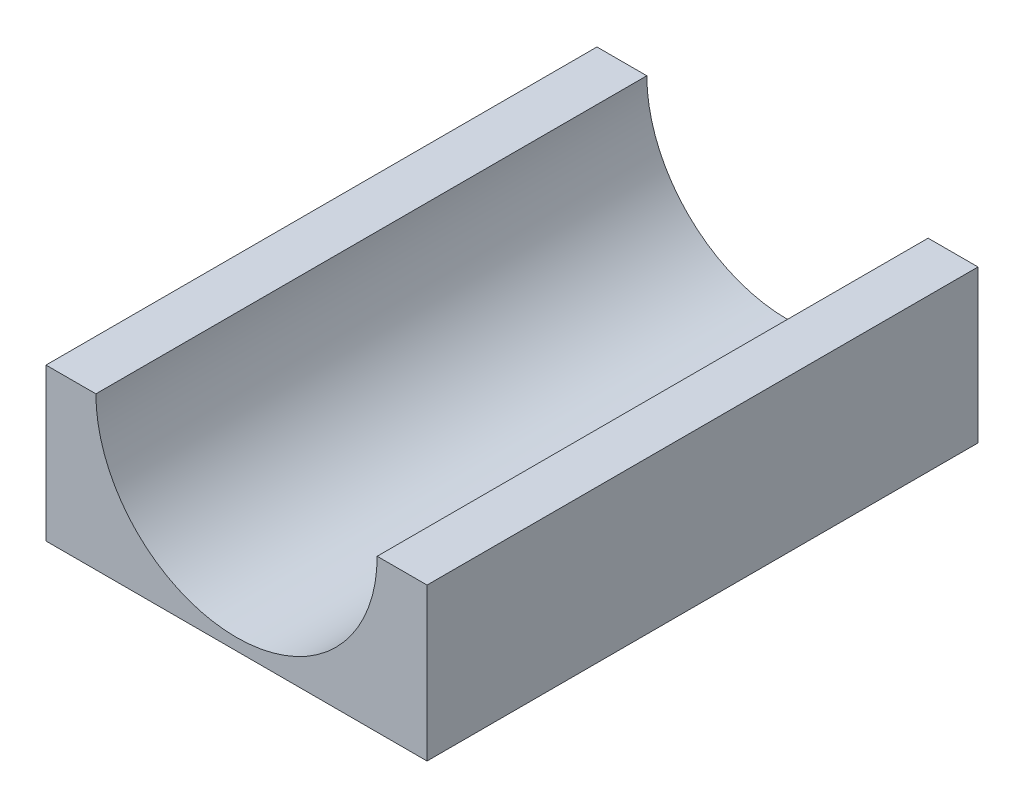
SolidWorks part; units mm, degrees
ref_plane "Front Plane" through (0, 0, 0) normal (0, 0, 1) x (1, 0, 0)
ref_plane "Top Plane" through (0, 0, 0) normal (0, 1, 0) x (1, 0, 0)
ref_plane "Right Plane" through (0, 0, 0) normal (1, 0, 0) x (0, 0, -1)
sketch "Sketch1" plane through (0, 0, 0) normal (0, 1, 0) x (1, 0, 0)
  line L1 (-25.4, 36.725) -> (25.4, 36.725)
  line L2 (-25.4, 36.725) -> (-25.4, -36.725)
  line L3 (-25.4, -36.725) -> (25.4, -36.725)
  line L4 (25.4, 36.725) -> (25.4, -36.725)
  point P4 (0, 36.725)
  point P6 (25.4, 0)
  dimension "D1" = 73.45
  dimension "D2" = 50.8
extrude "Boss-Extrude1" add sketch "Sketch1" along normal blind 20.32
sketch "Sketch2" plane through (0, 0, 36.725) normal (0, 0, 1) x (1, 0, 0)
  line L0 (-25.4, 20.32) -> (25.4, 20.32) construction
  circle A0 centre (0, 20.32) radius 18.75
  dimension "D1" = 37.5
extrude "Cut-Extrude1" cut sketch "Sketch2" against normal up to next
